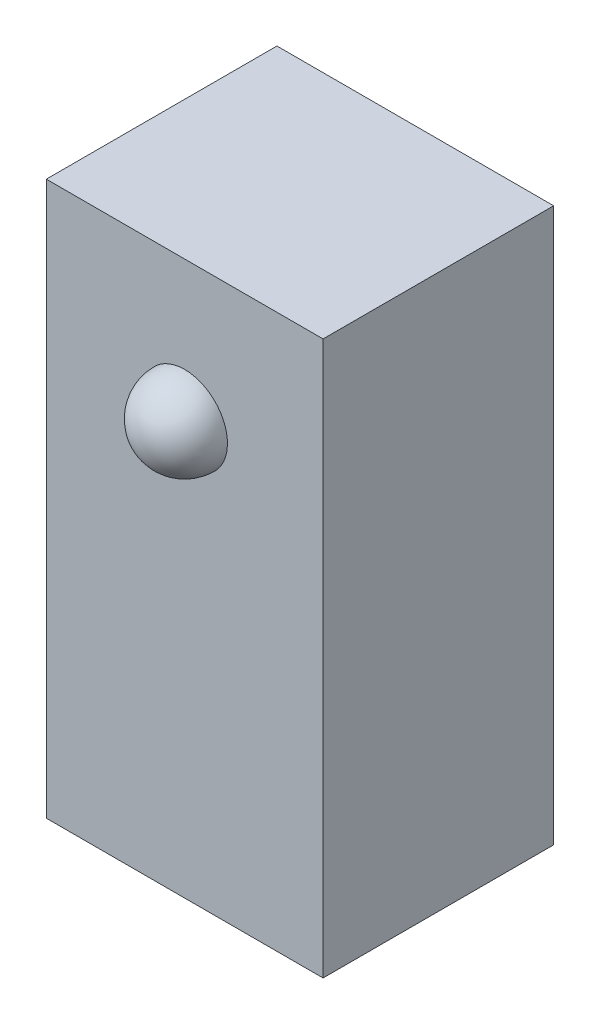
SolidWorks part; units mm, degrees
ref_plane "Front" through (0, 0, 0) normal (0, 0, 1) x (1, 0, 0)
ref_plane "Top" through (0, 0, 0) normal (0, 1, 0) x (1, 0, 0)
ref_plane "Right" through (0, 0, 0) normal (1, 0, 0) x (0, 0, -1)
sketch "Sketch1" plane through (0, 0, 0) normal (0, 1, 0) x (1, 0, 0)
  line L1 (-4.7625, -3.9688) -> (4.7625, -3.9688)
  line L2 (-4.7625, -3.9688) -> (-4.7625, 3.9688)
  line L3 (-4.7625, 3.9688) -> (4.7625, 3.9688)
  line L4 (4.7625, -3.9688) -> (4.7625, 3.9688)
  line L5 (-4.7625, -3.9688) -> (4.7625, 3.9688) construction
  line L6 (-4.7625, 3.9688) -> (4.7625, -3.9688) construction
  point P0 (0, 0)
  dimension "D1" = 9.525
  dimension "D2" = 7.9375
extrude "Boss-Extrude1" add sketch "Sketch1" along normal blind 19.05
sketch "Sketch2" plane through (0, 0, 3.9688) normal (0, 0, 1) x (1, 0, 0)
  line L0 (-4.7625, 0) -> (4.7625, 0) construction
  circle A0 centre (0, 14.2875) radius 1.1906
  dimension "D1" = 2.3813
  dimension "D2" = 14.2875
sketch "Sketch3" plane through (0, 0, 0) normal (1, 0, 0) x (0, 0, -1)
  line L0 (-3.9688, 14.2875) -> (-3.9688, 15.759)
  line L1 (-3.9688, 15.4781) -> (-3.9688, 13.0969) construction
  line L2 (-3.9688, 19.05) -> (-3.9688, 0) construction
  line L3 (-3.9688, 14.2875) -> (-5.4402, 14.2875)
  arc A0 (-3.9688, 15.759) -> (-5.4402, 14.2875) centre (-3.9688, 14.2875) ccw
revolve "Revolve1" add sketch "Sketch3" angle 360 about L3
